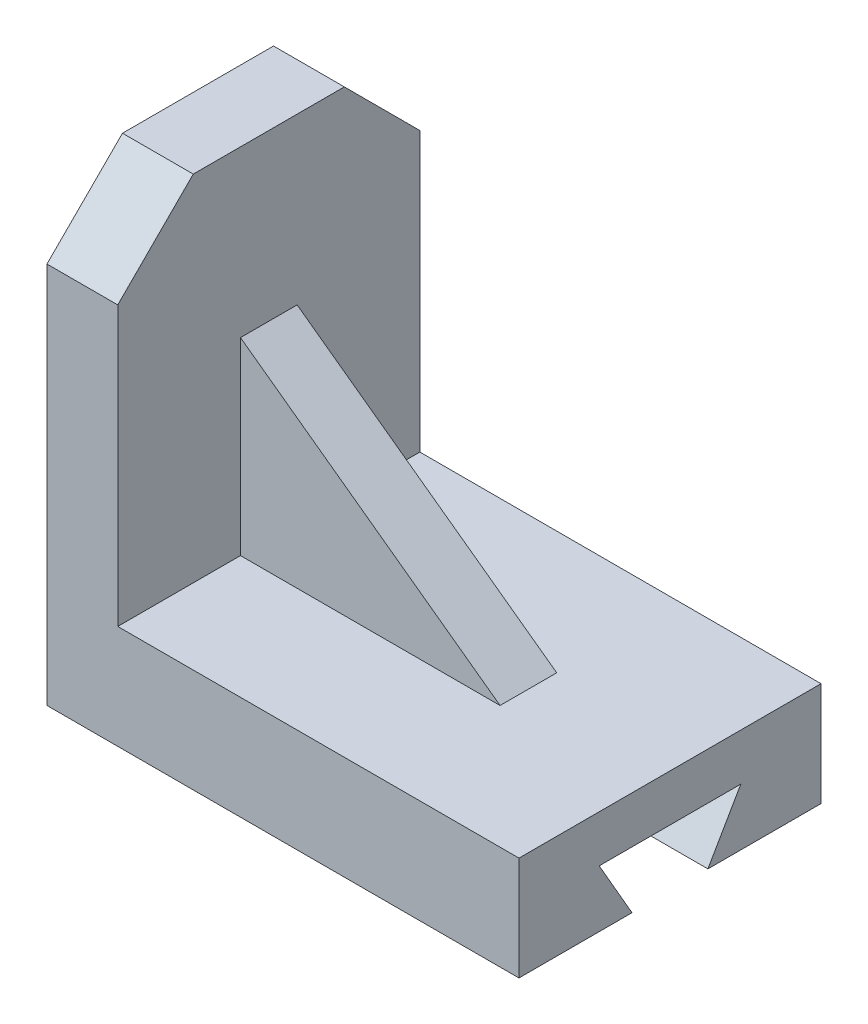
SolidWorks part; units mm, degrees
ref_plane "Front Plane" through (0, 0, 0) normal (0, 0, 1) x (1, 0, 0)
ref_plane "Top Plane" through (0, 0, 0) normal (0, 1, 0) x (1, 0, 0)
ref_plane "Right Plane" through (0, 0, 0) normal (1, 0, 0) x (0, 0, -1)
sketch "Sketch2" plane through (0, 0, 0) normal (0, 1, 0) x (1, 0, 0)
  line L1 (-73.8523, 27.8305) -> (26.1477, 27.8305)
  line L2 (-73.8523, 27.8305) -> (-73.8523, -36.1695)
  line L3 (-73.8523, -36.1695) -> (26.1477, -36.1695)
  line L4 (26.1477, 27.8305) -> (26.1477, -36.1695)
extrude "Boss-Extrude1" add sketch "Sketch2" along normal blind 22
sketch "Sketch3" plane through (-73.8523, 0, 0) normal (-1, 0, 0) x (0, 0, 1)
  line L0 (19.1695, 12.0733) -> (12.2177, 0)
  line L2 (-10.8305, 12.0733) -> (-3.86, 0)
  line L5 (-10.8305, 12.0733) -> (19.1695, 12.0733)
  line L7 (-3.86, 0) -> (12.2177, 0)
extrude "Cut-Extrude1" cut sketch "Sketch3" against normal blind 126
sketch "Sketch4" plane through (0, 22, 0) normal (0, 1, 0) x (1, 0, 0)
  line L0 (-73.8523, -36.1695) -> (26.1477, -36.1695) construction
  line L1 (-73.8523, 27.8305) -> (-58.8523, 27.8305)
  line L2 (-73.8523, 27.8305) -> (-73.8523, -36.1695)
  line L3 (-73.8523, -36.1695) -> (-58.8523, -36.1695)
  line L4 (-58.8523, 27.8305) -> (-58.8523, -36.1695)
extrude "Boss-Extrude2" add sketch "Sketch4" along normal blind 75
chamfer "Chamfer1" distance 16 1 edges at (-66.3523, 97, 36.1695)
chamfer "Chamfer2" distance 16 1 edges at (-66.3523, 97, -27.8305)
ref_plane "Plane3" through (0, 0, 4.1695) normal (0, 0, 1) x (1, 0, 0)
sketch "Sketch10" plane through (0, 0, 4.1695) normal (0, 0, 1) x (1, 0, 0)
  line L1 (-58.8523, 22) -> (26.1477, 22) construction
  line L3 (-58.8523, 81) -> (-58.8523, 22) construction
  line L4 (-58.8523, 62) -> (-3.8523, 22)
rib "Rib2" sketch "Sketch10" sketch "Sketch10" thickness 12 extrusion direction parallel to sketch draft on no parameters "D1"=12
